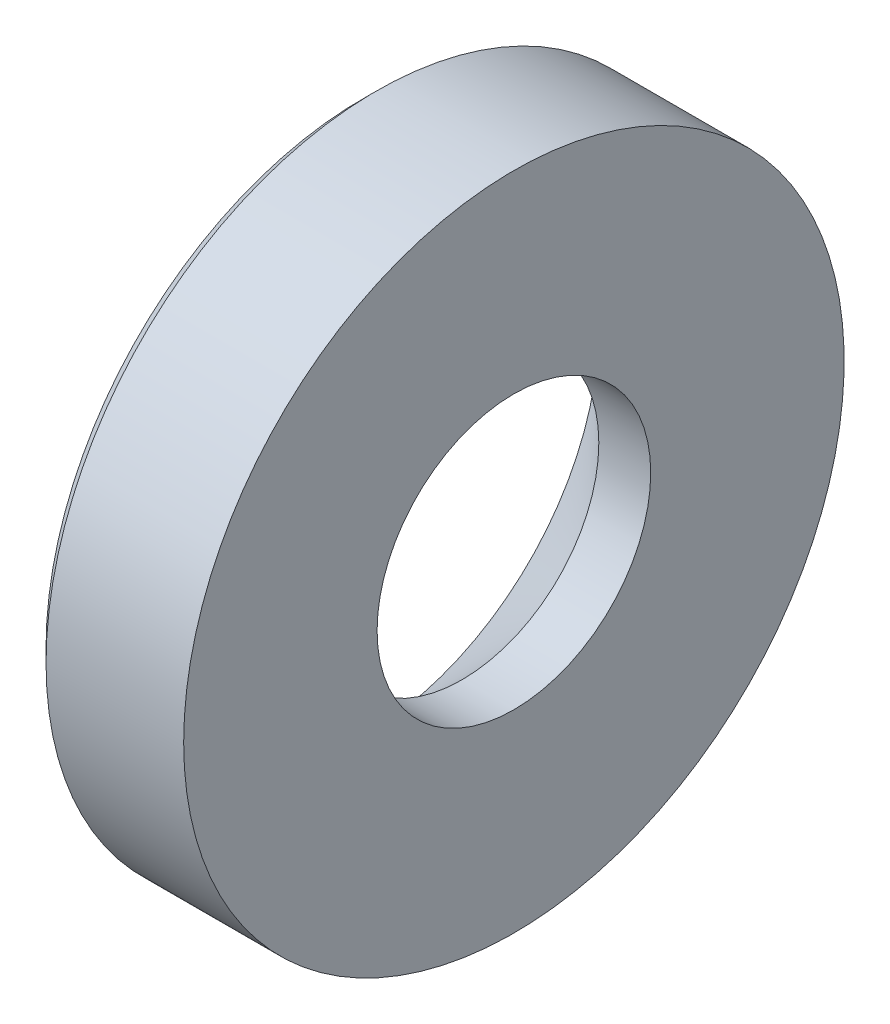
SolidWorks part; units mm, degrees
ref_plane "Front Plane" through (0, 0, 0) normal (0, 0, 1) x (1, 0, 0)
ref_plane "Top Plane" through (0, 0, 0) normal (0, 1, 0) x (1, 0, 0)
ref_plane "Right Plane" through (0, 0, 0) normal (1, 0, 0) x (0, 0, -1)
sketch "Sketch1" plane through (0, 0, 0) normal (0, 0, 1) x (1, 0, 0)
  line L0 (-58.7539, 0) -> (133.1684, 0) construction
  line L1 (37.2249, 7.25) -> (34.4749, 7.25)
  line L2 (37.2249, 9.7022) -> (37.2249, 17.5)
  line L3 (37.2249, 17.5) -> (29.932, 17.5)
  line L4 (34.4749, 7.25) -> (29.2249, 12.5)
  line L5 (29.2249, 12.5) -> (29.2249, 16.7929)
  line L6 (29.2249, 16.7929) -> (29.932, 17.5)
  line L8 (37.2249, 7.25) -> (37.2249, 9.7022)
  dimension "D1" = 7.25
  dimension "D2" = 17.5
  dimension "D3" = 2.75
  dimension "D4" = 12.5
  dimension "D5" = 45
  dimension "D6" = 1
  dimension "D7" = 45
revolve "Revolve1" add sketch "Sketch1" angle 360 about L0
